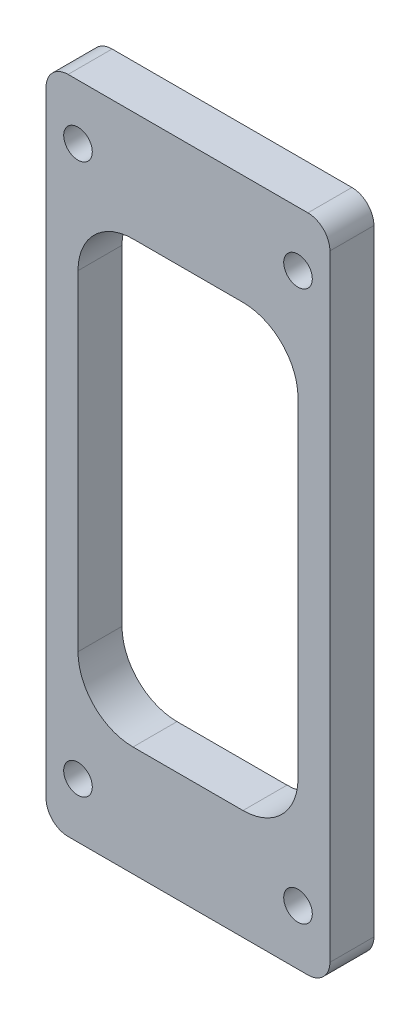
SolidWorks part; units mm, degrees
material "PLA"
ref_plane "Płaszczyzna przednia" through (0, 0, 0) normal (0, 0, 1) x (1, 0, 0)
ref_plane "Płaszczyzna górna" through (0, 0, 0) normal (0, 1, 0) x (1, 0, 0)
ref_plane "Płaszczyzna prawa" through (0, 0, 0) normal (1, 0, 0) x (0, 0, -1)
sketch "Szkic1" plane through (0, 0, 0) normal (0, 0, 1) x (1, 0, 0)
  line L1 (-12.9, 30) -> (12.9, 30)
  line L2 (-12.9, 30) -> (-12.9, -30)
  line L3 (-12.9, -30) -> (12.9, -30)
  line L4 (12.9, 30) -> (12.9, -30)
  line L5 (-12.9, 30) -> (12.9, -30) construction
  line L6 (-12.9, -30) -> (12.9, 30) construction
  point P0 (0, 0)
  dimension "D1" = 25.8
  dimension "D2" = 60
extrude "Dodanie-wyciągnięcie1" add sketch "Szkic1" along normal blind 4
sketch "Szkic2" plane through (0, 0, 4) normal (0, 0, 1) x (1, 0, 0)
  line L1 (-10, 25) -> (10, 25)
  line L2 (-10, 25) -> (-10, -25)
  line L3 (-10, -25) -> (10, -25)
  line L4 (10, 25) -> (10, -25)
  line L5 (-10, 25) -> (10, -25) construction
  line L6 (-10, -25) -> (10, 25) construction
  point P0 (0, 0)
  dimension "D1" = 20
  dimension "D2" = 50
hole_wizard "Otwór pod śrubę M21" positions "Szkic3" profile "Szkic4" hole size "M2" standard "ISO" end condition through all
sketch "Szkic3" plane through (0, 0, 4) normal (0, 0, 1) x (1, 0, 0)
  point P0 (-10, 25)
  point P3 (10, 25)
  point P6 (10, -25)
  point P9 (-10, -25)
sketch "Szkic4" plane through (-10, 25, 4) normal (1, 0, 0) x (0, -1, 0)
  line L0 (0, 0) -> (0, 4)
  line L1 (0, 4) -> (1.3, 4)
  line L2 (1.3, 4) -> (1.3, 0)
  line L5 (1.3, 0) -> (0, 0)
  line L11 (0, -6.35) -> (0, 107.95) construction
  dimension "Średnica otworu na wylot" = 2.6
  dimension "Głębokość otworu na wylot" = 4
fillet "Zaokrąglenie1" radius 2 4 edges at (-12.9, -30, 2) (-12.9, 30, 2) (12.9, -30, 2) (12.9, 30, 2)
sketch "Szkic5" plane through (0, 0, 4) normal (0, 0, 1) x (1, 0, 0)
  line L1 (5, 20) -> (-5, 20)
  line L2 (10, 15) -> (10, -15)
  line L3 (5, -20) -> (-5, -20)
  line L4 (-10, 15) -> (-10, -15)
  line L5 (10, 20) -> (-10, -20) construction
  line L6 (10, -20) -> (-10, 20) construction
  arc A0 (5, 20) -> (10, 15) centre (5, 15) cw
  arc A1 (-5, 20) -> (-10, 15) centre (-5, 15) ccw
  arc A2 (5, -20) -> (10, -15) centre (5, -15) ccw
  arc A3 (-5, -20) -> (-10, -15) centre (-5, -15) cw
  point P0 (0, 0)
  dimension "D3" = 5
  dimension "D4" = 5
  dimension "D5" = 5
  dimension "D6" = 5
  dimension "D1" = 40
  dimension "D2" = 20
extrude "Wytnij-wyciągnięcie1" cut sketch "Szkic5" against normal up to next
